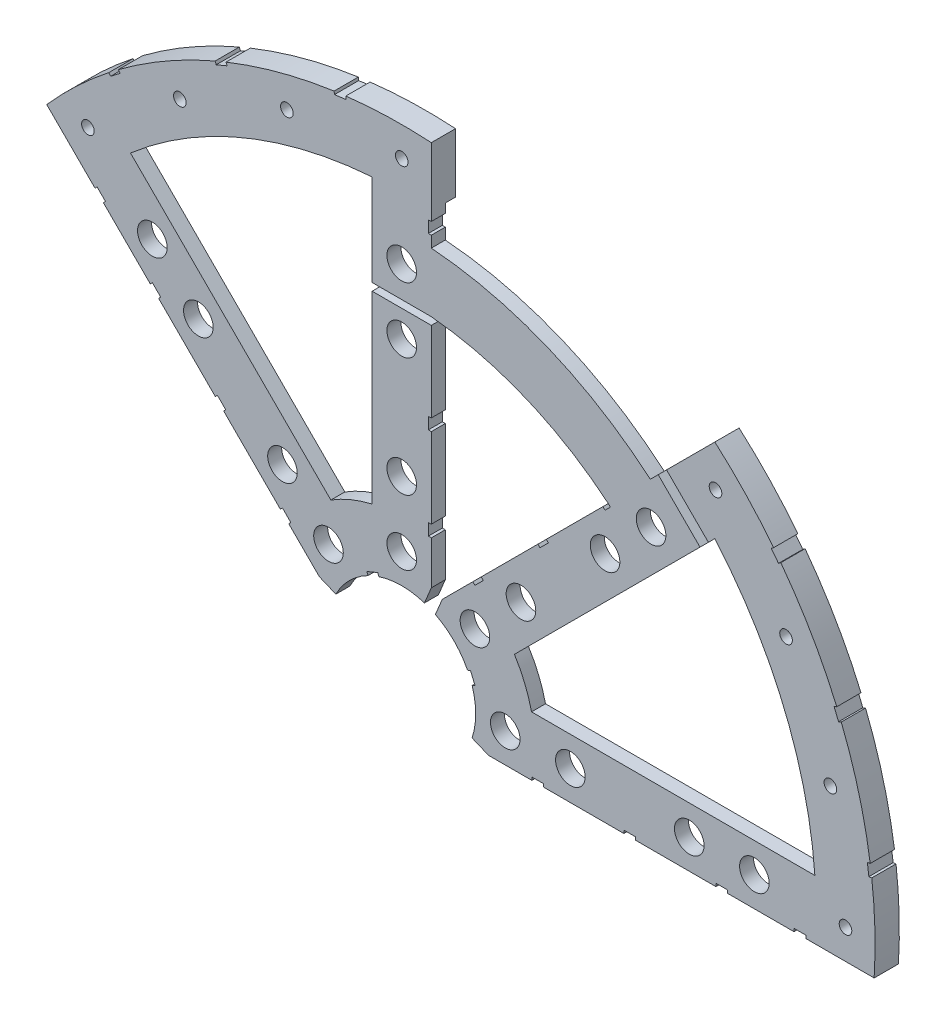
SolidWorks part; units mm, degrees
material "Brass"
ref_plane "Front Plane" through (0, 0, 0) normal (0, 0, 1) x (1, 0, 0)
ref_plane "Top Plane" through (0, 0, 0) normal (0, 1, 0) x (1, 0, 0)
ref_plane "Right Plane" through (0, 0, 0) normal (1, 0, 0) x (0, 0, -1)
sketch "Sketch1" plane through (0, 0, 0) normal (0, 0, 1) x (1, 0, 0)
  line L0 (0, 0) -> (320.3893, 0) construction
  line L1 (0, 0) -> (155.5285, 155.5285) construction
  line L2 (8.6967, 17.6769) -> (44.336, 53.3163)
  line L3 (8.6967, 17.6769) -> (7.229, 14.1336)
  line L4 (101.4014, -6.35) -> (18.6489, -6.35)
  line L5 (15.1056, -4.8823) -> (18.6489, -6.35)
  line L6 (88.6729, 6.35) -> (27.8605, 6.35)
  line L7 (-76.1917, 67.2115) -> (-17.6769, 8.6967)
  line L8 (-58.2111, 67.1914) -> (-15.2102, 24.1905)
  line L9 (67.1914, 58.2111) -> (24.1905, 15.2102)
  line L10 (0, 0) -> (40.4486, 97.6516) construction
  line L11 (0, 0) -> (123.4567, -51.1374) construction
  line L12 (-6.35, 88.6729) -> (-6.35, 27.8605)
  line L13 (-17.6769, 8.6967) -> (-14.1336, 7.229)
  line L14 (4.8823, 15.1056) -> (6.35, 18.6489)
  line L15 (6.35, 18.6489) -> (6.35, 69.0506)
  line L16 (0, 0) -> (15.1056, -4.8823) construction
  line L17 (0, 0) -> (4.8823, 15.1056) construction
  line L18 (8.6967, 17.6769) -> (13.294, 8.6183) construction
  line L19 (18.6489, -6.35) -> (15.4943, 3.3063) construction
  line L20 (27.8605, 6.35) -> (27.7442, 6.7059) construction
  line L21 (24.1905, 15.2102) -> (24.3599, 14.8764) construction
  line L22 (6.35, 101.4014) -> (6.35, 18.6489) [skipped]
  line L23 (6.35, 81.7959) -> (6.35, 101.4014)
  line L24 (53.3483, 62.3286) -> (67.2115, 76.1917)
  line L25 (67.2115, 76.1917) -> (8.6967, 17.6769) construction
  arc A0 (7.229, 14.1336) -> (15.1056, -4.8823) centre (0, 0) cw
  arc A1 (67.2115, 76.1917) -> (101.4014, -6.35) centre (0, 0) cw
  arc A2 (24.1905, 15.2102) -> (27.8605, 6.35) centre (0, 0) cw
  arc A3 (67.1914, 58.2111) -> (88.6729, 6.35) centre (0, 0) cw
  arc A4 (-76.1917, 67.2115) -> (6.35, 101.4014) centre (0, 0) cw
  arc A5 (-58.2111, 67.1914) -> (-6.35, 88.6729) centre (0, 0) cw
  arc A6 (-15.2102, 24.1905) -> (-6.35, 27.8605) centre (0, 0) cw
  arc A7 (-14.1336, 7.229) -> (4.8823, 15.1056) centre (0, 0) cw
  arc A8 (13.294, 8.6183) -> (15.4943, 3.3063) centre (0, 0) cw construction
  arc A9 (24.3599, 14.8764) -> (27.7442, 6.7059) centre (0, 0) cw construction
  arc A10 (53.3483, 62.3286) -> (6.35, 81.7959) centre (0, 0) ccw
  arc A11 (44.336, 53.3163) -> (6.35, 69.0506) centre (0, 0) ccw
  dimension "D1" = 45
  dimension "D3" = 6.35
  dimension "D4" = 15.875
  dimension "D7" = 22.5
  dimension "D8" = 101.6
  dimension "D11" = 12.7
  dimension "D12" = 12.7
  dimension "D15" = 82.042
  dimension "D16" = 12.7
  dimension "D2" = 6.35
  dimension "D5" = 67.5
  dimension "D9" = 1.27
  dimension "D10" = 1.27
  dimension "D14" = 90
  dimension "D6" = 12.7
  dimension "D13" = 2
extrude "Boss-Extrude1" add sketch "Sketch1" along normal blind 3
sketch "Sketch4" plane through (0, 0, 0) normal (0, 0, -1) x (-1, 0, 0)
  line L0 (76.1917, 67.2115) -> (17.6769, 8.6967) construction
  line L1 (-6.35, 81.7959) -> (-6.35, 101.4014) construction
  line L2 (-67.2115, 76.1917) -> (-53.3483, 62.3286) construction
  line L3 (-18.6489, -6.35) -> (-101.4014, -6.35) construction
  line L4 (67.1914, 58.2111) -> (76.1917, 67.2115)
  line L5 (-6.35, 88.6729) -> (-6.35, 101.4014)
  line L6 (-58.2111, 67.1914) -> (-67.2115, 76.1917)
  line L7 (-88.6729, -6.35) -> (-101.4014, -6.35)
  arc A0 (76.1917, 67.2115) -> (-6.35, 101.4014) centre (0, 0) ccw
  arc A1 (76.1917, 67.2115) -> (-6.35, 101.4014) centre (0, 0) ccw construction
  arc A2 (67.1914, 58.2111) -> (-6.35, 88.6729) centre (0, 0) ccw
  arc A3 (-58.2111, 67.1914) -> (-88.6729, -6.35) centre (0, 0) ccw
  arc A4 (-67.2115, 76.1917) -> (-101.4014, -6.35) centre (0, 0) ccw
  arc A5 (-67.2115, 76.1917) -> (-101.4014, -6.35) centre (0, 0) ccw construction
extrude "Boss-Extrude2" add sketch "Sketch4" along normal blind 2.207
sketch "Sketch2" plane through (0, 0, 3) normal (0, 0, 1) x (1, 0, 0)
  line L0 (0, 0) -> (101.6, 0) construction
  line L1 (0, 0) -> (22.225, 0) construction
  line L2 (0, 0) -> (15.7154, 15.7154) construction
  line L3 (67.1914, 58.2111) -> (24.1905, 15.2102) construction
  arc A0 (101.4014, -6.35) -> (67.2115, 76.1917) centre (0, 0) ccw construction
  circle A1 centre (22.225, 0) radius 3.175
  arc A2 (15.1056, -4.8823) -> (7.229, 14.1336) centre (0, 0) ccw construction
  circle A3 centre (36.195, 0) radius 3.175
  circle A4 centre (61.722, 0) radius 3.175
  circle A5 centre (75.692, 0) radius 3.175
  circle A6 centre (53.5223, 53.5223) radius 3.175
  circle A7 centre (43.644, 43.644) radius 3.175
  circle A8 centre (25.5937, 25.5937) radius 3.175
  circle A9 centre (15.7154, 15.7154) radius 3.175
  circle A10 centre (0, 75.692) radius 3.175
  circle A11 centre (0, 61.722) radius 3.175
  circle A12 centre (0, 36.195) radius 3.175
  circle A13 centre (0, 22.225) radius 3.175
  circle A14 centre (-53.5223, 53.5223) radius 3.175
  circle A15 centre (-43.644, 43.644) radius 3.175
  circle A16 centre (-25.5937, 25.5937) radius 3.175
  circle A17 centre (-15.7154, 15.7154) radius 3.175
  arc A18 (4.8823, 15.1056) -> (-14.1336, 7.229) centre (0, 0) ccw construction
  dimension "D3" = 6.35
  dimension "D2" = 6.35
  dimension "D5" = 13.97
  dimension "D7" = 13.97
  dimension "D4" = 25.527
  dimension "D1" = 45
  dimension "D8" = 6.35
  dimension "D9" = 6.35
  dimension "D6" = 4
extrude "Cut-Extrude1" cut sketch "Sketch2" against normal through all
sketch "Sketch3" plane through (0, 0, 3) normal (0, 0, 1) x (1, 0, 0)
  line L0 (15.2664, 24.2467) -> (17.0625, 26.0427)
  line L1 (15.2664, 24.2467) -> (15.7154, 23.7977)
  line L2 (17.0625, 26.0427) -> (17.5115, 25.5937)
  line L3 (15.7154, 23.7977) -> (17.5115, 25.5937)
  line L4 (55.049, 64.0292) -> (56.845, 65.8253)
  line L5 (44.336, 53.3163) -> (8.6967, 17.6769) construction
  line L6 (29.2307, 38.211) -> (31.0268, 40.007)
  line L7 (29.2307, 38.211) -> (29.6797, 37.762)
  line L8 (31.0268, 40.007) -> (31.4758, 39.558)
  line L9 (27.94, -6.35) -> (30.48, -6.35)
  line L10 (27.94, -6.35) -> (27.94, -5.715)
  line L11 (30.48, -6.35) -> (30.48, -5.715)
  line L12 (27.94, -5.715) -> (30.48, -5.715)
  line L13 (18.6489, -6.35) -> (101.4014, -6.35) construction
  line L14 (67.437, -6.35) -> (69.977, -6.35)
  line L15 (67.437, -6.35) -> (67.437, -5.715)
  line L16 (69.977, -6.35) -> (69.977, -5.715)
  line L17 (67.437, -5.715) -> (69.977, -5.715)
  line L18 (29.6797, 37.762) -> (31.4758, 39.558)
  line L19 (55.049, 64.0292) -> (64.0566, 55.0216)
  line L20 (56.845, 65.8253) -> (65.8527, 56.8176)
  line L21 (64.0566, 55.0216) -> (65.8527, 56.8176)
  line L22 (67.2115, 76.1917) -> (53.3483, 62.3286) construction
  line L23 (-65.8253, 56.845) -> (-64.0292, 55.049)
  line L24 (43.195, 52.1753) -> (44.336, 53.3163)
  line L25 (43.195, 52.1753) -> (43.644, 51.7263)
  line L26 (47.6885, -6.35) -> (50.2285, -6.35)
  line L27 (47.6885, -6.35) -> (47.6885, -5.715)
  line L28 (50.2285, -6.35) -> (50.2285, -5.715)
  line L29 (47.6885, -5.715) -> (50.2285, -5.715)
  line L30 (84.201, -6.35) -> (86.741, -6.35)
  line L31 (84.201, -6.35) -> (84.201, -5.715)
  line L32 (86.741, -6.35) -> (86.741, -5.715)
  line L33 (84.201, -5.715) -> (86.741, -5.715)
  line L34 (0, 0) -> (100.7308, 13.2615) construction
  line L35 (0, 0) -> (93.8662, 38.8806) construction
  line L36 (0, 0) -> (80.6047, 61.8502) construction
  line L37 (0, 0) -> (101.6, 0) construction
  line L38 (99.9355, 14.4377) -> (100.267, 11.9194)
  line L39 (99.9355, 14.4377) -> (101.1946, 14.6035)
  line L40 (100.267, 11.9194) -> (101.5261, 12.0852)
  line L41 (101.1946, 14.6035) -> (101.5261, 12.0852)
  line L42 (99.9355, 14.4377) -> (101.5261, 12.0852) construction
  line L43 (100.267, 11.9194) -> (101.1946, 14.6035) construction
  line L44 (93.7655, 37.4643) -> (94.9388, 37.9503)
  line L45 (93.7655, 37.4643) -> (92.7935, 39.811)
  line L46 (94.9388, 37.9503) -> (93.9668, 40.297)
  line L47 (92.7935, 39.811) -> (93.9668, 40.297)
  line L48 (93.7655, 37.4643) -> (93.9668, 40.297) construction
  line L49 (94.9388, 37.9503) -> (92.7935, 39.811) construction
  line L50 (79.3278, 62.4712) -> (80.874, 60.456)
  line L51 (79.3278, 62.4712) -> (80.3354, 63.2443)
  line L52 (80.874, 60.456) -> (81.8816, 61.2292)
  line L53 (80.3354, 63.2443) -> (81.8816, 61.2292)
  line L54 (79.3278, 62.4712) -> (81.8816, 61.2292) construction
  line L55 (80.874, 60.456) -> (80.3354, 63.2443) construction
  line L56 (13.5939, 7.0054) -> (14.5659, 4.6588)
  line L57 (13.5939, 7.0054) -> (14.7672, 7.4914)
  line L58 (14.5659, 4.6588) -> (15.7393, 5.1448)
  line L59 (14.7672, 7.4914) -> (15.7393, 5.1448)
  line L60 (13.5939, 7.0054) -> (15.7393, 5.1448) construction
  line L61 (14.5659, 4.6588) -> (14.7672, 7.4914) construction
  line L62 (44.336, 53.3163) -> (44.7851, 52.8673)
  line L63 (43.644, 51.7263) -> (44.7851, 52.8673)
  line L64 (-24.2467, 15.2664) -> (-26.0427, 17.0625)
  line L65 (-24.2467, 15.2664) -> (-23.7977, 15.7154)
  line L66 (-26.0427, 17.0625) -> (-25.5937, 17.5115)
  line L67 (-23.7977, 15.7154) -> (-25.5937, 17.5115)
  line L68 (-40.007, 31.0268) -> (-38.211, 29.2307)
  line L69 (-40.007, 31.0268) -> (-39.558, 31.4758)
  line L70 (-38.211, 29.2307) -> (-37.762, 29.6797)
  line L71 (-39.558, 31.4758) -> (-37.762, 29.6797)
  line L72 (-65.8253, 56.845) -> (-65.3763, 57.294)
  line L73 (-64.0292, 55.049) -> (-63.5802, 55.498)
  line L74 (-65.3763, 57.294) -> (-63.5802, 55.498)
  line L76 (-63.2443, 80.3354) -> (-61.2292, 81.8816)
  line L77 (-62.4712, 79.3278) -> (-61.2292, 81.8816) construction
  line L78 (-60.456, 80.874) -> (-63.2443, 80.3354) construction
  line L79 (-62.4712, 79.3278) -> (-63.2443, 80.3354)
  line L80 (-60.456, 80.874) -> (-61.2292, 81.8816)
  line L81 (-62.4712, 79.3278) -> (-60.456, 80.874)
  line L82 (-37.9503, 94.9388) -> (-40.297, 93.9668)
  line L83 (-37.4643, 93.7655) -> (-40.297, 93.9668) construction
  line L84 (-37.9503, 94.9388) -> (-39.811, 92.7935) construction
  line L85 (-39.811, 92.7935) -> (-40.297, 93.9668)
  line L86 (-37.4643, 93.7655) -> (-37.9503, 94.9388)
  line L87 (-37.4643, 93.7655) -> (-39.811, 92.7935)
  line L88 (-14.4377, 99.9355) -> (-14.6035, 101.1946)
  line L89 (-14.4377, 99.9355) -> (-11.9194, 100.267)
  line L90 (-14.4377, 99.9355) -> (-12.0852, 101.5261) construction
  line L91 (-11.9194, 100.267) -> (-14.6035, 101.1946) construction
  line L92 (-11.9194, 100.267) -> (-12.0852, 101.5261)
  line L93 (-14.6035, 101.1946) -> (-12.0852, 101.5261)
  line L94 (5.715, 84.201) -> (5.715, 86.741)
  line L95 (6.35, 86.741) -> (5.715, 86.741)
  line L96 (6.35, 84.201) -> (6.35, 86.741)
  line L97 (6.35, 84.201) -> (5.715, 84.201)
  line L98 (5.715, 47.6885) -> (5.715, 50.2285)
  line L99 (6.35, 47.6885) -> (6.35, 50.2285)
  line L100 (6.35, 47.6885) -> (5.715, 47.6885)
  line L101 (6.35, 50.2285) -> (5.715, 50.2285)
  line L102 (5.715, 27.94) -> (5.715, 30.48)
  line L103 (6.35, 27.94) -> (6.35, 30.48)
  line L104 (6.35, 30.48) -> (5.715, 30.48)
  line L105 (6.35, 27.94) -> (5.715, 27.94)
  line L106 (-7.4914, 14.7672) -> (-5.1448, 15.7393)
  line L107 (-7.0054, 13.5939) -> (-5.1448, 15.7393) construction
  line L108 (-4.6588, 14.5659) -> (-7.4914, 14.7672) construction
  line L109 (-7.0054, 13.5939) -> (-4.6588, 14.5659)
  line L110 (-7.0054, 13.5939) -> (-7.4914, 14.7672)
  line L111 (-4.6588, 14.5659) -> (-5.1448, 15.7393)
  line L112 (0, 0) -> (14.5659, 4.6588) construction
  line L113 (0, 0) -> (-4.6588, 14.5659) construction
  line L114 (6.35, 69.0506) -> (6.35, 67.437)
  line L115 (6.35, 69.0506) -> (-6.3731, 69.0506)
  line L116 (6.35, 67.437) -> (-6.3731, 67.437)
  line L117 (-6.3731, 69.0506) -> (-6.3731, 67.437)
  line L118 (6.35, 18.6489) -> (6.35, 69.0506) construction
  line L120 (-53.9713, 44.9911) -> (-52.1753, 43.195)
  line L121 (-53.9713, 44.9911) -> (-53.5223, 45.4401)
  line L122 (-52.1753, 43.195) -> (-51.7263, 43.644)
  line L123 (-53.5223, 45.4401) -> (-51.7263, 43.644)
  line L124 (-76.1917, 67.2115) -> (-17.6769, 8.6967) construction
  line L125 (-38.211, 29.2307) -> (-40.007, 31.0268) [skipped]
  line L126 (-40.007, 31.0268) -> (-39.558, 31.4758) [skipped]
  line L127 (-37.762, 29.6797) -> (-39.558, 31.4758) [skipped]
  line L128 (-38.211, 29.2307) -> (-37.762, 29.6797) [skipped]
  line L129 (-26.0427, 17.0625) -> (-25.5937, 17.5115) [skipped]
  line L130 (-23.7977, 15.7154) -> (-25.5937, 17.5115) [skipped]
  line L131 (-24.2467, 15.2664) -> (-26.0427, 17.0625) [skipped]
  line L132 (-24.2467, 15.2664) -> (-23.7977, 15.7154) [skipped]
  circle A0 centre (-53.5223, 53.5223) radius 3.175 construction
  circle A1 centre (0, 22.225) radius 3.175 construction
  circle A2 centre (22.225, 0) radius 3.175 construction
  circle A3 centre (61.722, 0) radius 3.175 construction
  arc A4 (101.4014, -6.35) -> (67.2115, 76.1917) centre (0, 0) ccw construction
  circle A5 centre (-15.7154, 15.7154) radius 3.175 construction
  circle A6 centre (-25.5937, 25.5937) radius 3.175 construction
  circle A7 centre (-43.644, 43.644) radius 3.175 construction
  arc A9 (15.1056, -4.8823) -> (7.229, 14.1336) centre (0, 0) ccw construction
  circle A12 centre (15.7154, 15.7154) radius 3.175 construction
  circle A14 centre (43.644, 43.644) radius 3.175 construction
  circle A15 centre (36.195, 0) radius 3.175 construction
  circle A16 centre (25.5937, 25.5937) radius 3.175 construction
  circle A17 centre (0, 61.722) radius 3.175 construction
  arc A18 (4.8823, 15.1056) -> (-14.1336, 7.229) centre (0, 0) ccw construction
  circle A22 centre (53.5223, 53.5223) radius 3.175 construction
  circle A23 centre (75.692, 0) radius 3.175 construction
  point P75 (14.6666, 6.0751)
  dimension "D8" = 0.635
  dimension "D9" = 5.715
  dimension "D12" = 5.715
  dimension "D4" = 7.5
  dimension "D5" = 22.5
  dimension "D7" = 37.5
  dimension "D10" = 90
  dimension "D11" = 1.27
  dimension "D14" = 0.635
  dimension "D15" = 90
  dimension "D18" = 0.635
  dimension "D19" = 90
  dimension "D22" = 0.635
  dimension "D20" = 1.27
  dimension "D17" = 0.635
  dimension "D25" = 90
  dimension "D26" = 2.54
  dimension "D29" = 2.54
  dimension "D3" = 5.715
  dimension "D21" = 5.715
  dimension "D28" = 5.715
  dimension "D6" = 11.4935
  dimension "D23" = 11.4935
  dimension "D27" = 5.715
  dimension "D30" = 0.635
  dimension "D13" = 8.509
  dimension "D16" = 8.509
  dimension "D33" = 90
  dimension "D32" = 8.509
  dimension "D34" = 2.54
  dimension "D35" = 2.54
  dimension "D31" = 5.715
  dimension "D36" = 5.715
  dimension "D37" = 11.4935
  dimension "D24" = 2
extrude "Cut-Extrude2" cut sketch "Sketch3" against normal through all
hole_wizard "#6-32 Tapped Hole1" positions "Sketch6" profile "Sketch5" tap size "#6-32" standard "ANSI Inch" end condition through all
sketch "Sketch6" plane through (0, 0, 3) normal (0, 0, 1) x (1, 0, 0)
  line L0 (0, 0) -> (95.25, 0) construction
  line L2 (86.741, -6.35) -> (101.4014, -6.35) construction
  line L3 (0, 0) -> (95.25, 0) construction
  line L4 (0, 0) -> (92.0044, 24.6525) construction
  line L5 (67.2115, 76.1917) -> (56.845, 65.8253) construction
  arc A0 (101.4014, -6.35) -> (100.8887, 12.0013) centre (0, 0) ccw construction
  arc A1 (6.35, 101.4014) -> (-12.0013, 100.8887) centre (0, 0) ccw construction
  circle A2 centre (53.5223, 53.5223) radius 3.175 construction
  point P0 (95.25, 0)
  point P28 (92.0044, 24.6525)
  point P29 (82.4889, 47.625)
  point P30 (67.3519, 67.3519)
  point P31 (47.625, 82.4889) [skipped]
  point P32 (24.6525, 92.0044) [skipped]
  point P33 (0, 95.25)
  point P34 (-24.6525, 92.0044)
  point P35 (-47.625, 82.4889)
  point P36 (-67.3519, 67.3519)
  dimension "D1" = 6.35
  dimension "D2" = 6.35
  dimension "D4" = 15
  dimension "D5" = 6.35
  dimension "D6" = 6.35
  dimension "D7" = 19.558
  dimension "D3" = 10
cosmetic thread "Hole Thread1" parameters "D2"=3.5052
cosmetic thread "Hole Thread2" parameters "D2"=3.5052
cosmetic thread "Hole Thread3" parameters "D2"=3.5052
cosmetic thread "Hole Thread4" parameters "D2"=3.5052
cosmetic thread "Hole Thread5" parameters "D2"=3.5052
cosmetic thread "Hole Thread6" parameters "D2"=3.5052
cosmetic thread "Hole Thread7" parameters "D2"=3.5052
cosmetic thread "Hole Thread8" parameters "D2"=3.5052
sketch "Sketch5" plane through (95.25, 0, 3) normal (1, 0, 0) x (0, -1, 0)
  line L0 (0, 0) -> (0, 5.207)
  line L1 (0, 5.207) -> (1.3525, 5.207)
  line L2 (1.3525, 5.207) -> (1.3525, 0)
  line L5 (1.3525, 0) -> (0, 0)
  line L11 (0, -6.35) -> (0, 107.95) construction
  dimension "Thru Tap Drill Dia." = 2.7051
  dimension "Thru Tap Drill Depth" = 5.207
equation "\"LayerH\"= 3mm"
equation "\"D1@Boss-Extrude1\"=\"LayerH\""
equation "\"D1@Boss-Extrude2\"=.205-\"LayerH\""
equation "\"CoilSep\"= 1.005"
equation "\"D4@Sketch2\"=\"CoilSep\""
equation "\"D6@Sketch3\"=\"CoilSep\"/2-.05"
equation "\"D23@Sketch3\"=\"CoilSep\"/2-.05"
equation "\"CoilSep2\"= 0.770in"
equation "\"D13@Sketch3\"=\"CoilSep2\"/2-.05"
equation "\"D16@Sketch3\"=\"CoilSep2\"/2-.05"
equation "\"D32@Sketch3\"=\"CoilSep2\"/2-.05"
equation "\"D37@Sketch3\"=\"CoilSep\"/2-.05"
